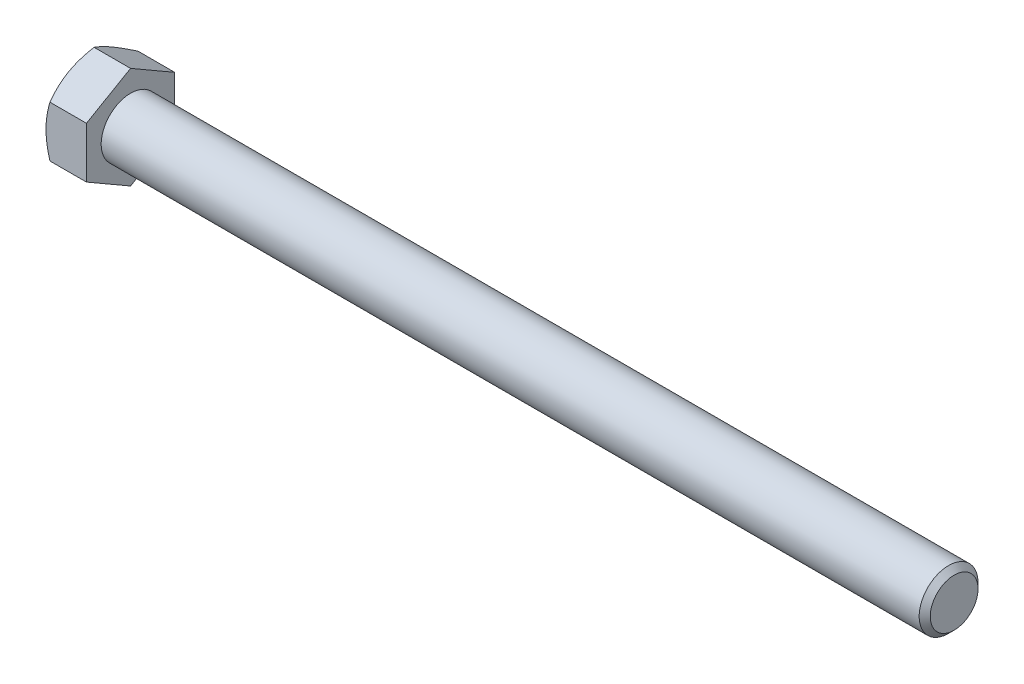
SolidWorks part; units mm, degrees
material "Alloy Steel"
ref_plane "Front Plane" through (0, 0, 0) normal (0, 0, 1) x (1, 0, 0)
ref_plane "Top Plane" through (0, 0, 0) normal (0, 1, 0) x (1, 0, 0)
ref_plane "Right Plane" through (0, 0, 0) normal (1, 0, 0) x (0, 0, -1)
sketch "Sketch1" plane through (0, 0, 0) normal (0, 0, 1) x (1, 0, 0)
  line L0 (-93.2656, 0) -> (93.2656, 0) construction
  line L1 (93.2656, 6.35) -> (93.2656, -6.35) construction
  line L2 (-84.5344, 9.525) -> (-84.5344, -9.525) construction
  line L3 (-93.2656, 9.525) -> (-93.2656, -9.525) construction
  point P9 (-84.5344, 0)
  point P10 (86.4272, -6.35)
  dimension "Screw Dia" = 12.7
  dimension "Hex" = 19.05
  dimension "Head Ht" = 8.7312
  dimension "Screw Lenght" = 177.8
  dimension "D1" = 6.8385
ref_plane "Plane2" through (93.2656, 0, 0) normal (1, 0, 0) x (0, 0, -1)
sketch "Sketch5" plane through (93.2656, 0, 0) normal (1, 0, 0) x (0, 0, -1)
  circle A0 centre (0, 0) radius 6.35
extrude "Boss-Extrude3" add sketch "Sketch5" against normal up to vertex (177.8 mm away) up to point (-84.5344, 0, 0)
sketch "Sketch9" plane through (93.2656, 0, 0) normal (1, 0, 0) x (0, 0, -1)
  circle A1 centre (0, 0) radius 6.35
  circle A2 centre (0, 0) radius 6.35
  dimension "D1" = 0
curve "Helix/Spiral1" pitch 1.9538 height 179.7538 turns 92 parameters "Pitch"=1.9538
chamfer "Chamfer1" distance 1.1958 angle 45 1 edges at (93.2656, 0, -6.35)
sketch "Sketch10" plane through (0, 0, 0) normal (0, 0, 1) x (1, 0, 0)
  line L0 (93.2656, 6.35) -> (93.9983, 5.0809)
  line L1 (93.9983, 5.0809) -> (94.2425, 5.0809)
  line L2 (94.2425, 5.0809) -> (94.9752, 6.35)
  line L3 (93.2656, 6.35) -> (94.9752, 6.35)
  line L4 (94.1204, 6.35) -> (94.1204, 5.0809) construction
  line L5 (93.632, 5.7155) -> (94.6089, 5.7155) construction
  dimension "D1" = 60
  dimension "D2" = 0.2442
  dimension "D3" = 0.9769
sketch "Sketch6" plane through (-84.5344, 0, 0) normal (-1, 0, 0) x (0, 0, 1)
  line L0 (0, 9.525) -> (0, -9.525) construction
  line L1 (9.525, 5.4993) -> (0, 10.9985)
  line L2 (0, 10.9985) -> (-9.525, 5.4993)
  line L3 (-9.525, 5.4993) -> (-9.525, -5.4993)
  line L4 (-9.525, -5.4993) -> (0, -10.9985)
  line L5 (0, -10.9985) -> (9.525, -5.4993)
  line L6 (9.525, -5.4993) -> (9.525, 5.4993)
  circle A0 centre (0, 0) radius 9.525 construction
extrude "Boss-Extrude4" add sketch "Sketch6" along normal up to vertex (8.7312 mm away) up to point (-93.2656, -9.525, 0)
sketch "Sketch7" plane through (-93.2656, 0, 0) normal (-1, 0, 0) x (0, 0, 1)
  circle A0 centre (0, 0) radius 9.525 construction
  circle A1 centre (0, 0) radius 9.525
sketch "Sketch8" plane through (-93.2656, 0, 0) normal (-1, 0, 0) x (0, 0, 1)
  circle A0 centre (0, 0) radius 9.525 construction
  circle A1 centre (0, 0) radius 9.525
extrude "Cut-Extrude3" cut sketch "Sketch8" against normal through all draft 60 flip side to cut
sketch "Sketch12" plane through (-93.2656, 0, 0) normal (-1, 0, 0) x (0, 0, 1)
  line L0 (0, 7.3343) -> (0, 4.0958) construction
  line L1 (0.2858, 7.3343) -> (0.2858, 4.0958)
  line L2 (-0.2858, 7.3343) -> (-0.2857, 4.0958)
  line L3 (0, 6.35) -> (0, -6.35) construction
  arc A0 (0.2858, 7.3343) -> (-0.2858, 7.3343) centre (0, 7.3343) ccw
  arc A1 (-0.2857, 4.0958) -> (0.2858, 4.0958) centre (0, 4.0958) ccw
  circle A3 centre (0, 0) radius 3.81 construction
  circle A4 centre (0, 0) radius 7.62 construction
  point P2 (0, 5.715)
  dimension "D1" = 7.62
  dimension "D3" = 15.24
  dimension "D2" = 0.5715
extrude "Cut-Extrude4" cut sketch "Sketch12" against normal blind 0.254
pattern_circular "CirPattern1" count 3 over 360 about axis through (0, 0, 0) along (1, 0, 0) of "Cut-Extrude4"
equation "\"D2@Sketch10\" = \"Pitch@Helix/Spiral1\"*.125"
equation "\"D3@Sketch10\" = \"Pitch@Helix/Spiral1\"*.5"
equation "\"D1@Chamfer1\" = \"Pitch@Helix/Spiral1\"*.612"
equation "\"D1@Sketch12\" = \"Hex@Sketch1\"*.4"
equation "\"D3@Sketch12\" = \"Hex@Sketch1\"*.8"
equation "\"D2@Sketch12\" = \"Hex@Sketch1\"*.03"
equation "\"D1@Sketch1\" = \"Pitch@Helix/Spiral1\"*3.5"
equation "\"D3@Helix/Spiral1\" = \"Screw Lenght@Sketch1\"+\"Pitch@Helix/Spiral1\""
